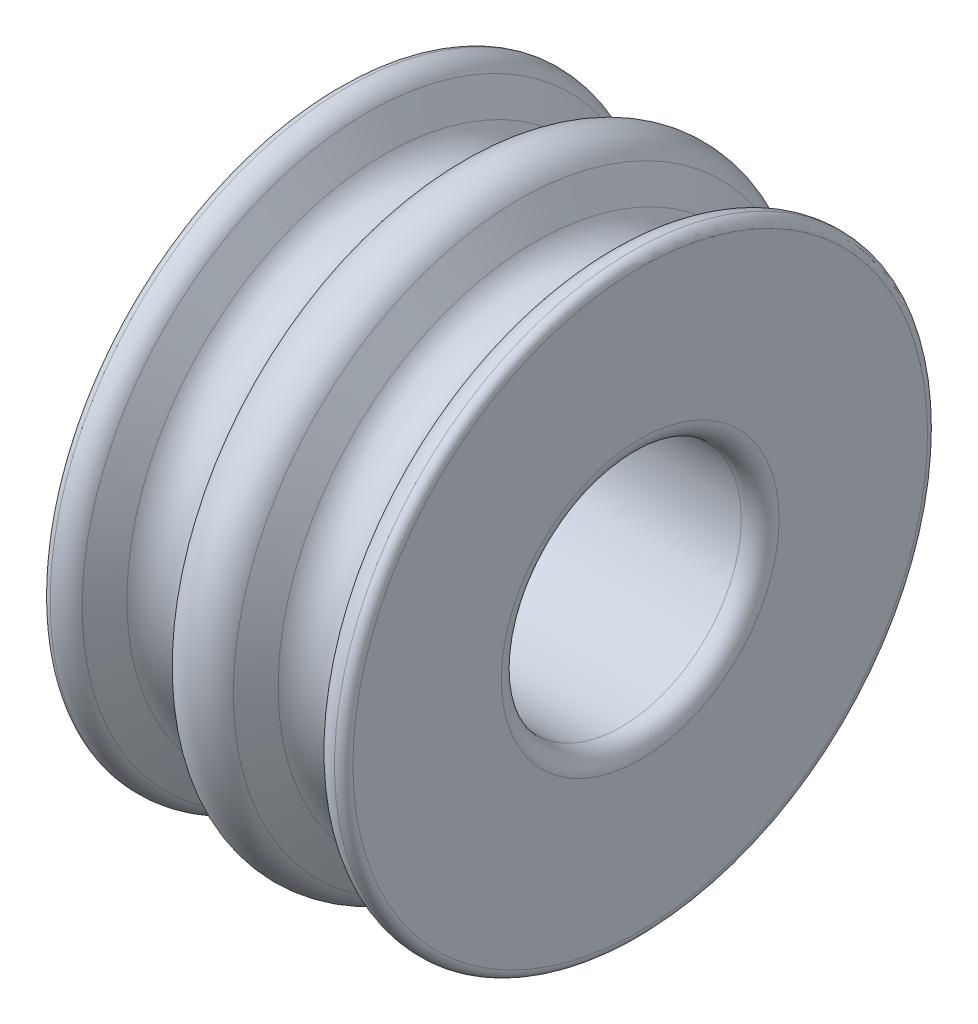
SolidWorks part; units mm, degrees
ref_plane "Front Plane" through (0, 0, 0) normal (0, 0, 1) x (1, 0, 0)
ref_plane "Top Plane" through (0, 0, 0) normal (0, 1, 0) x (1, 0, 0)
ref_plane "Right Plane" through (0, 0, 0) normal (1, 0, 0) x (0, 0, -1)
sketch "Sketch1" plane through (0, 0, 0) normal (0, 0, 1) x (1, 0, 0)
  line L0 (-8, 12.7) -> (-8, 15.2006)
  line L1 (8, 0) -> (-8, 0)
  line L2 (0, 0) -> (0, 12.7) construction
  line L3 (0, 12.7) -> (-8, 12.7) construction
  line L4 (-8, 0) -> (-8, 12.7)
  line L5 (-6.4257, 15.1015) -> (-5.5588, 13.6)
  line L6 (-2.4412, 13.6) -> (-1.5743, 15.1015)
  line L7 (0, 15.2006) -> (0, 12.7) construction
  line L8 (2.4412, 13.6) -> (1.5743, 15.1015)
  line L9 (6.4257, 15.1015) -> (5.5588, 13.6)
  line L10 (8, 0) -> (8, 12.7)
  line L11 (8, 12.7) -> (8, 15.2006)
  arc A0 (-8, 15.2006) -> (-7.525, 15.7) centre (-7.5, 15.2006) cw
  arc A1 (-7.525, 15.7) -> (-6.4257, 15.1015) centre (-7.465, 14.5015) cw
  arc A2 (-5.5588, 13.6) -> (-2.4412, 13.6) centre (-4, 14.5) ccw
  arc A3 (-1.5743, 15.1015) -> (-0.475, 15.7) centre (-0.535, 14.5015) cw construction
  arc A4 (-0.475, 15.7) -> (0, 15.2006) centre (-0.5, 15.2006) cw construction
  arc A5 (0.475, 15.7) -> (0, 15.2006) centre (0.5, 15.2006) ccw construction
  arc A6 (1.5743, 15.1015) -> (0.475, 15.7) centre (0.535, 14.5015) ccw construction
  arc A7 (5.5588, 13.6) -> (2.4412, 13.6) centre (4, 14.5) cw
  arc A8 (7.525, 15.7) -> (6.4257, 15.1015) centre (7.465, 14.5015) ccw
  arc A9 (8, 15.2006) -> (7.525, 15.7) centre (7.5, 15.2006) ccw
  arc A10 (-1.5743, 15.1015) -> (1.5743, 15.1015) centre (0, 14.1926) cw
  point P21 (0.5, 15.7)
  point P22 (1.5743, 15.1498)
  point P26 (-4, 12.7)
  point P27 (-4, 12.7)
  dimension "D4" = 0.5
  dimension "D5" = 1.2
  dimension "D6" = 1.8
  dimension "D1" = 12.7
  dimension "D2" = 8
  dimension "D3" = 3
  dimension "D7" = 60
revolve "Revolve1" add sketch "Sketch1" angle 360 about L1
sketch "Sketch2" plane through (8, 0, 0) normal (1, 0, 0) x (0, 0, -1)
  circle A0 centre (0, 0) radius 6.35
  dimension "D1" = 12.7
extrude "Cut-Extrude1" cut sketch "Sketch2" against normal through all
fillet "Fillet1" radius 1 2 edges at (-8, 0, -6.35) (8, 0, -6.35)
